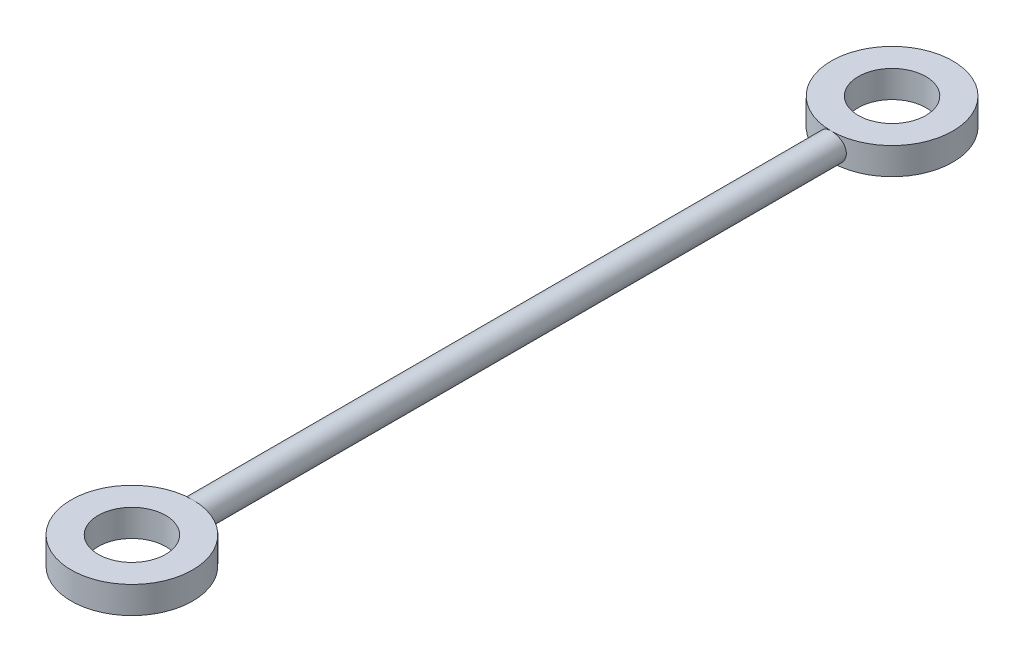
SolidWorks part; units mm, degrees
ref_plane "Front Plane" through (0, 0, 0) normal (0, 0, 1) x (1, 0, 0)
ref_plane "Top Plane" through (0, 0, 0) normal (0, 1, 0) x (1, 0, 0)
ref_plane "Right Plane" through (0, 0, 0) normal (1, 0, 0) x (0, 0, -1)
sketch "Sketch1" plane through (0, 0, 0) normal (0, 0, 1) x (1, 0, 0)
  circle A0 centre (0, 0) radius 10
  dimension "D1" = 20
extrude "Boss-Extrude1" add sketch "Sketch1" along normal blind 493
sketch "Sketch2" plane through (0, 0, 0) normal (1, 0, 0) x (0, 0, -1)
  line L0 (-493, 10) -> (-493, -10) construction
  line L1 (-493, 0) -> (-528, 0) construction
  line L2 (-528, 0) -> (-528, 50) construction
  line L4 (-483, -10) -> (-503, -10)
  line L5 (-483, -10) -> (-483, 10)
  line L6 (-483, 10) -> (-503, 10)
  line L7 (-503, -10) -> (-503, 10)
  line L8 (-483, -10) -> (-503, 10) construction
  line L9 (-483, 10) -> (-503, -10) construction
  dimension "D2" = 50
  dimension "D3" = 35
sketch "Sketch3" plane through (0, 0, 0) normal (1, 0, 0) x (0, 0, -1)
  line L0 (0, 0) -> (35, 0) construction
  line L1 (35, 0) -> (35, 50) construction
  line L2 (-493, -10) -> (0, -10) construction
  line L3 (10, 10) -> (-10, 10)
  line L4 (10, 10) -> (10, -10)
  line L5 (10, -10) -> (-10, -10)
  line L6 (-10, 10) -> (-10, -10)
  line L7 (10, 10) -> (-10, -10) construction
  line L8 (10, -10) -> (-10, 10) construction
  point P1 (0, 0)
  point P12 (18.0011, 10)
  point P13 (0, 0)
  point P14 (0, 0)
  dimension "D1" = 50
  dimension "D2" = 35
revolve "Revolve1" add sketch "Sketch2" angle 360 about L2
revolve "Revolve2" add sketch "Sketch3" angle 360 about L1
